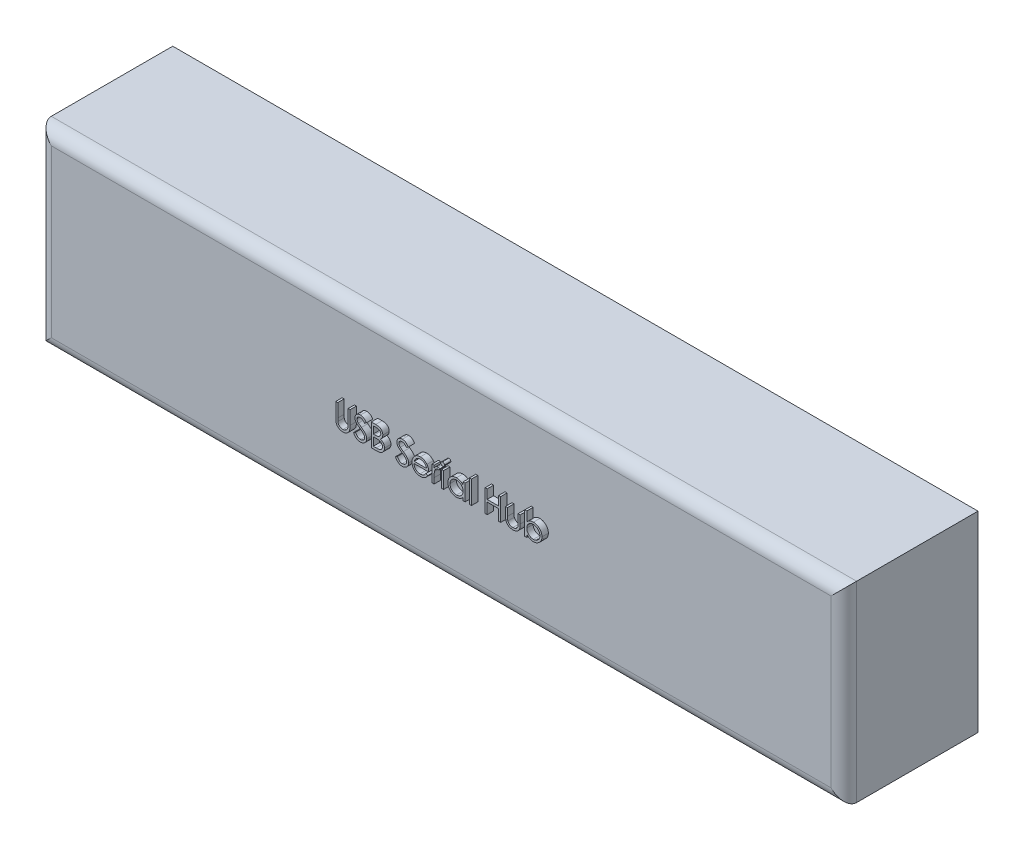
SolidWorks part; units mm, degrees
ref_plane "Front Plane" through (0, 0, 0) normal (0, 0, 1) x (1, 0, 0)
ref_plane "Top Plane" through (0, 0, 0) normal (0, 1, 0) x (1, 0, 0)
ref_plane "Right Plane" through (0, 0, 0) normal (1, 0, 0) x (0, 0, -1)
sketch "Sketch1" plane through (0, 0, 0) normal (0, 0, 1) x (1, 0, 0)
  line L1 (-63, -15) -> (63, -15)
  line L2 (-63, -15) -> (-63, 15)
  line L3 (-63, 15) -> (63, 15)
  line L4 (63, -15) -> (63, 15)
  line L5 (0, 15) -> (0, -15) construction
  line L6 (-63, 0) -> (63, 0) construction
  point P0 (0, 0)
  dimension "D1" = 126
  dimension "D2" = 30
extrude "Boss-Extrude1" add sketch "Sketch1" along normal blind 21
fillet "Fillet1" radius 2 4 edges at (0, -15, 21) (-63, 0, 21) (0, 15, 21) (63, 0, 21)
sketch "Sketch2" plane through (0, 0, 21) normal (0, 0, 1) x (1, 0, 0)
  text T0 "USB Serial Hub"
extrude "Boss-Extrude2" add sketch "Sketch2" along normal blind 1
